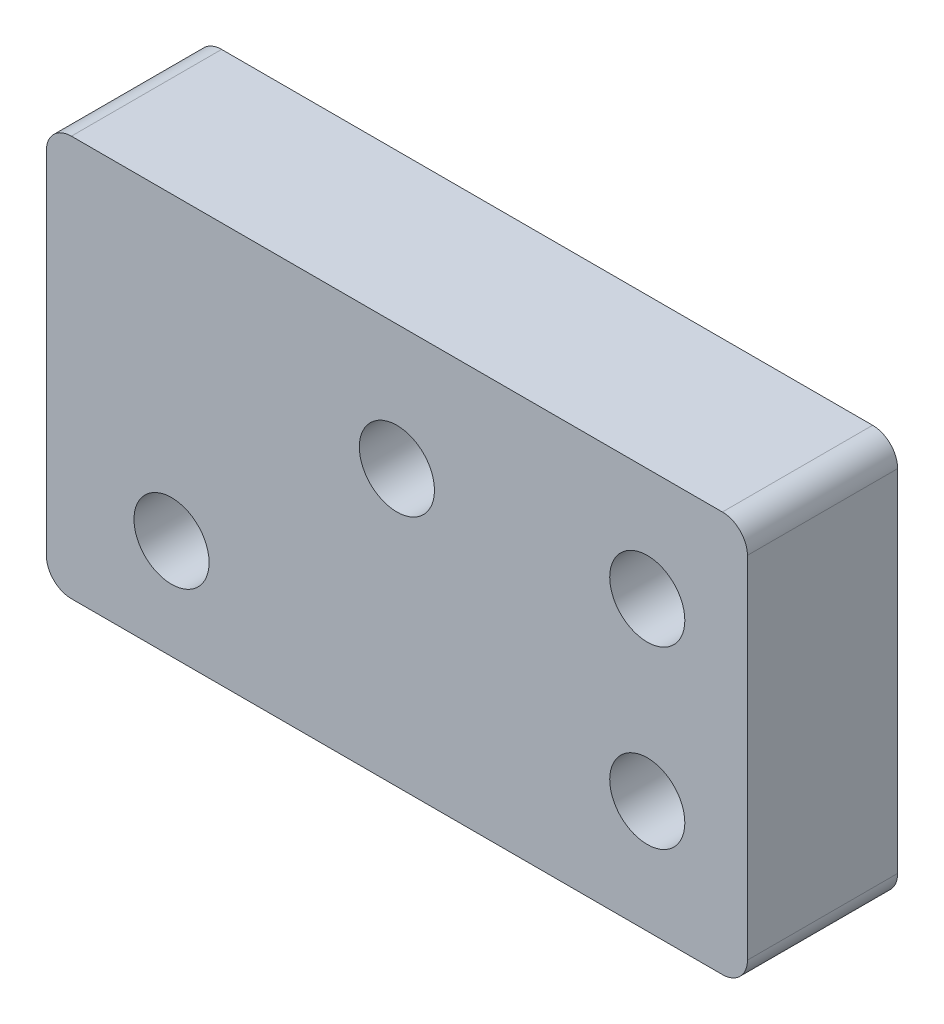
SolidWorks part; units mm, degrees
ref_plane "前视基准面" through (0, 0, 0) normal (0, 0, 1) x (1, 0, 0)
ref_plane "上视基准面" through (0, 0, 0) normal (0, 1, 0) x (1, 0, 0)
ref_plane "右视基准面" through (0, 0, 0) normal (1, 0, 0) x (0, 0, -1)
sketch "草图1" plane through (0, 0, 0) normal (0, 0, 1) x (1, 0, 0)
  line L1 (14, -8) -> (-14, -8)
  line L2 (14, -8) -> (14, 8)
  line L3 (14, 8) -> (-14, 8)
  line L4 (-14, -8) -> (-14, 8)
  line L5 (14, -8) -> (-14, 8) construction
  line L6 (14, 8) -> (-14, -8) construction
  point P0 (0, 0)
  dimension "D1" = 28
  dimension "D2" = 16
extrude "凸台-拉伸1" add sketch "草图1" along normal blind 6
sketch "草图2" plane through (0, 0, 0) normal (0, 0, -1) x (-1, 0, 0)
  line L0 (-10, -31) -> (-10, 18.7629) construction
  line L2 (-14, 8) -> (14, 8) construction
  line L3 (14, -8) -> (-14, -8) construction
  line L4 (-14, -8) -> (-14, 8) construction
  circle A0 centre (-10, 3.5) radius 2.85
  circle A1 centre (-10, -3.5) radius 2.85
  dimension "D1" = 5.7
  dimension "D2" = 5.7
  dimension "D4" = 4.5
  dimension "D5" = 4.5
  dimension "D3" = 4
extrude "切除-拉伸1" cut sketch "草图2" against normal blind 3.2
sketch "草图3" plane through (0, 0, 3.2) normal (0, 0, -1) x (-1, 0, 0)
  circle A0 centre (-10, 3.5) radius 1.5
  circle A1 centre (-10, -3.5) radius 1.5
  dimension "D1" = 3
  dimension "D2" = 3
extrude "切除-拉伸2" cut sketch "草图3" against normal blind 3.2
fillet "圆角1" radius 1 4 edges at (-14, 8, 3) (-14, -8, 3) (14, -8, 3) (14, 8, 3)
sketch "草图4" plane through (0, 0, 6) normal (0, 0, 1) x (1, 0, 0)
  line L0 (-13, -8) -> (13, -8) construction
  line L1 (-14, 7) -> (-14, -7) construction
  line L2 (14, -7) -> (14, 7) construction
  line L3 (13, 8) -> (-13, 8) construction
  circle A0 centre (0, 3) radius 1.5
  circle A1 centre (-9, -4) radius 1.5
  dimension "D1" = 3
  dimension "D2" = 3
  dimension "D3" = 4
  dimension "D4" = 5
  dimension "D5" = 14
  dimension "D6" = 5
extrude "切除-拉伸3" cut sketch "草图4" against normal blind 10
